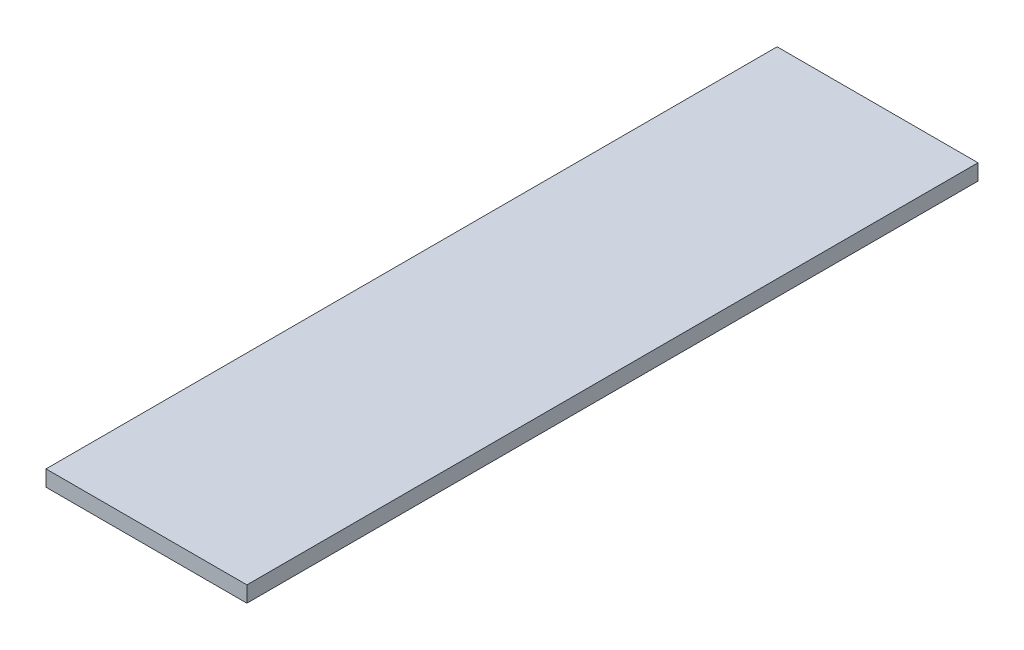
SolidWorks part; units mm, degrees
ref_plane "Front Plane" through (0, 0, 0) normal (0, 0, 1) x (1, 0, 0)
ref_plane "Top Plane" through (0, 0, 0) normal (0, 1, 0) x (1, 0, 0)
ref_plane "Right Plane" through (0, 0, 0) normal (1, 0, 0) x (0, 0, -1)
sketch "Sketch1" plane through (0, 0, 0) normal (0, 0, 1) x (1, 0, 0)
  line L1 (0, 0) -> (40.132, 0)
  line L2 (0, 0) -> (0, 3.175)
  line L3 (0, 3.175) -> (40.132, 3.175)
  line L4 (40.132, 0) -> (40.132, 3.175)
  dimension "D1" = 40.132
  dimension "D2" = 3.175
extrude "Boss-Extrude1" add sketch "Sketch1" along normal blind 146.05
